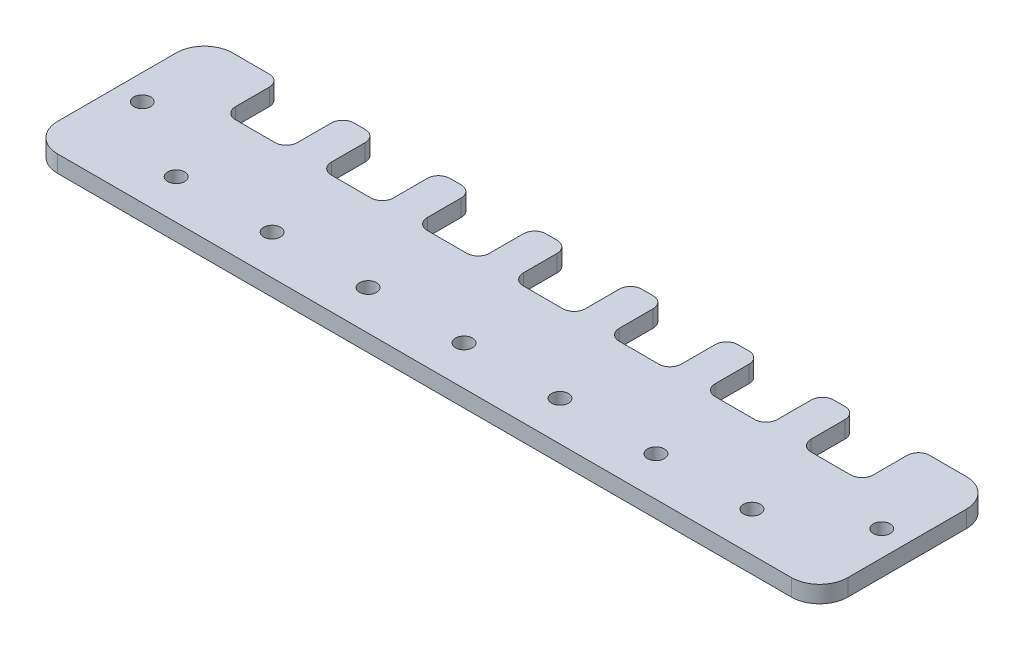
SolidWorks part; units mm, degrees
ref_plane "Front Plane" through (0, 0, 0) normal (0, 0, 1) x (1, 0, 0)
ref_plane "Top Plane" through (0, 0, 0) normal (0, 1, 0) x (1, 0, 0)
ref_plane "Right Plane" through (0, 0, 0) normal (1, 0, 0) x (0, 0, -1)
sketch "Sketch1" plane through (0, 0, 0) normal (0, 1, 0) x (1, 0, 0)
  line L0 (-70, -8.5) -> (70, -8.5) construction
  line L1 (65, 15.5) -> (58.5, 15.5)
  line L2 (70, 10.5) -> (70, -10.5)
  line L3 (65, -15.5) -> (-65, -15.5)
  line L4 (-70, 10.5) -> (-70, -10.5)
  line L5 (70, 15.5) -> (-70, -15.5) construction
  line L6 (70, -15.5) -> (-70, 15.5) construction
  line L7 (-70, 0) -> (70, 0) construction
  line L8 (0, 17.5) -> (0, -15.5) construction
  line L9 (-56.5, 7.5) -> (56.5, 7.5) construction
  line L10 (-54.5, 7.5) -> (-47.5, 7.5) construction
  line L12 (-54.5, 5.5) -> (-47.5, 5.5)
  line L15 (-58.5, 15.5) -> (-65, 15.5)
  line L18 (-51, -8.5) -> (-51, 7.5) construction
  line L21 (-37.5, 5.5) -> (-30.5, 5.5)
  line L24 (-39.5, 7.5) -> (-39.5, 13.5)
  line L27 (-28.5, 7.5) -> (-28.5, 13.5)
  line L30 (-37.5, 7.5) -> (-30.5, 7.5) construction
  line L31 (-20.5, 5.5) -> (-13.5, 5.5)
  line L32 (-56.5, 7.5) -> (-56.5, 13.5)
  line L33 (-45.5, 7.5) -> (-45.5, 13.5)
  line L34 (-22.5, 7.5) -> (-22.5, 13.5)
  line L35 (-11.5, 7.5) -> (-11.5, 13.5)
  line L36 (-20.5, 7.5) -> (-13.5, 7.5) construction
  line L37 (-3.5, 5.5) -> (3.5, 5.5)
  line L38 (-5.5, 7.5) -> (-5.5, 13.5)
  line L39 (5.5, 7.5) -> (5.5, 13.5)
  line L40 (-3.5, 7.5) -> (3.5, 7.5) construction
  line L41 (13.5, 5.5) -> (20.5, 5.5)
  line L42 (11.5, 7.5) -> (11.5, 13.5)
  line L43 (22.5, 7.5) -> (22.5, 13.5)
  line L44 (13.5, 7.5) -> (20.5, 7.5) construction
  line L45 (30.5, 5.5) -> (37.5, 5.5)
  line L46 (28.5, 7.5) -> (28.5, 13.5)
  line L47 (39.5, 7.5) -> (39.5, 13.5)
  line L48 (30.5, 7.5) -> (37.5, 7.5) construction
  line L49 (47.5, 5.5) -> (54.5, 5.5)
  line L50 (45.5, 7.5) -> (45.5, 13.5)
  line L51 (56.5, 7.5) -> (56.5, 13.5)
  line L52 (47.5, 7.5) -> (54.5, 7.5) construction
  line L53 (-41.5, 15.5) -> (-43.5, 15.5)
  line L54 (-24.5, 15.5) -> (-26.5, 15.5)
  line L55 (-7.5, 15.5) -> (-9.5, 15.5)
  line L56 (9.5, 15.5) -> (7.5, 15.5)
  line L57 (26.5, 15.5) -> (24.5, 15.5)
  line L58 (43.5, 15.5) -> (41.5, 15.5)
  circle A0 centre (-65.5, 0) radius 1.5
  circle A1 centre (65.5, 0) radius 1.5
  arc A2 (-56.5, 7.5) -> (-54.5, 5.5) centre (-54.5, 7.5) ccw
  arc A3 (-47.5, 5.5) -> (-45.5, 7.5) centre (-47.5, 7.5) ccw
  circle A16 centre (-51, -8.5) radius 1.5
  circle A17 centre (-34, -8.5) radius 1.5
  circle A18 centre (-17, -8.5) radius 1.5
  circle A19 centre (0, -8.5) radius 1.5
  circle A20 centre (17, -8.5) radius 1.5
  circle A21 centre (34, -8.5) radius 1.5
  circle A22 centre (51, -8.5) radius 1.5
  arc A23 (65, 15.5) -> (70, 10.5) centre (65, 10.5) cw
  arc A24 (70, -10.5) -> (65, -15.5) centre (65, -10.5) cw
  arc A25 (-65, -15.5) -> (-70, -10.5) centre (-65, -10.5) cw
  arc A26 (-65, 15.5) -> (-70, 10.5) centre (-65, 10.5) ccw
  arc A27 (-45.5, 13.5) -> (-43.5, 15.5) centre (-43.5, 13.5) cw
  arc A28 (-56.5, 13.5) -> (-58.5, 15.5) centre (-58.5, 13.5) ccw
  arc A29 (-39.5, 7.5) -> (-37.5, 5.5) centre (-37.5, 7.5) ccw
  arc A30 (-30.5, 5.5) -> (-28.5, 7.5) centre (-30.5, 7.5) ccw
  arc A31 (-28.5, 13.5) -> (-26.5, 15.5) centre (-26.5, 13.5) cw
  arc A32 (-39.5, 13.5) -> (-41.5, 15.5) centre (-41.5, 13.5) ccw
  arc A33 (-22.5, 7.5) -> (-20.5, 5.5) centre (-20.5, 7.5) ccw
  arc A34 (-13.5, 5.5) -> (-11.5, 7.5) centre (-13.5, 7.5) ccw
  arc A35 (-11.5, 13.5) -> (-9.5, 15.5) centre (-9.5, 13.5) cw
  arc A36 (-22.5, 13.5) -> (-24.5, 15.5) centre (-24.5, 13.5) ccw
  arc A37 (-5.5, 7.5) -> (-3.5, 5.5) centre (-3.5, 7.5) ccw
  arc A38 (3.5, 5.5) -> (5.5, 7.5) centre (3.5, 7.5) ccw
  arc A39 (5.5, 13.5) -> (7.5, 15.5) centre (7.5, 13.5) cw
  arc A40 (-5.5, 13.5) -> (-7.5, 15.5) centre (-7.5, 13.5) ccw
  arc A41 (11.5, 7.5) -> (13.5, 5.5) centre (13.5, 7.5) ccw
  arc A42 (20.5, 5.5) -> (22.5, 7.5) centre (20.5, 7.5) ccw
  arc A43 (22.5, 13.5) -> (24.5, 15.5) centre (24.5, 13.5) cw
  arc A44 (11.5, 13.5) -> (9.5, 15.5) centre (9.5, 13.5) ccw
  arc A45 (28.5, 7.5) -> (30.5, 5.5) centre (30.5, 7.5) ccw
  arc A46 (37.5, 5.5) -> (39.5, 7.5) centre (37.5, 7.5) ccw
  arc A47 (39.5, 13.5) -> (41.5, 15.5) centre (41.5, 13.5) cw
  arc A48 (28.5, 13.5) -> (26.5, 15.5) centre (26.5, 13.5) ccw
  arc A49 (45.5, 7.5) -> (47.5, 5.5) centre (47.5, 7.5) ccw
  arc A50 (54.5, 5.5) -> (56.5, 7.5) centre (54.5, 7.5) ccw
  arc A51 (56.5, 13.5) -> (58.5, 15.5) centre (58.5, 13.5) cw
  arc A52 (45.5, 13.5) -> (43.5, 15.5) centre (43.5, 13.5) ccw
  point P0 (0, 0)
  point P29 (-56.5, 15.5)
  dimension "D4" = 3
  dimension "D5" = 3
  dimension "D11" = 2
  dimension "D14" = 3
  dimension "D16" = 5
  dimension "D13" = 2
  dimension "D10" = 2
  dimension "D1" = 140
  dimension "D2" = 31
  dimension "D3" = 7
  dimension "D6" = 131
  dimension "D7" = 65.5
  dimension "D8" = 113
  dimension "D9" = 16
  dimension "D12" = 11
  dimension "D17" = 2
  dimension "D18" = 7
  dimension "D19" = 17
  dimension "D20" = 17
  dimension "D15" = 7
extrude "Boss-Extrude1" add sketch "Sketch1" along normal blind 3
